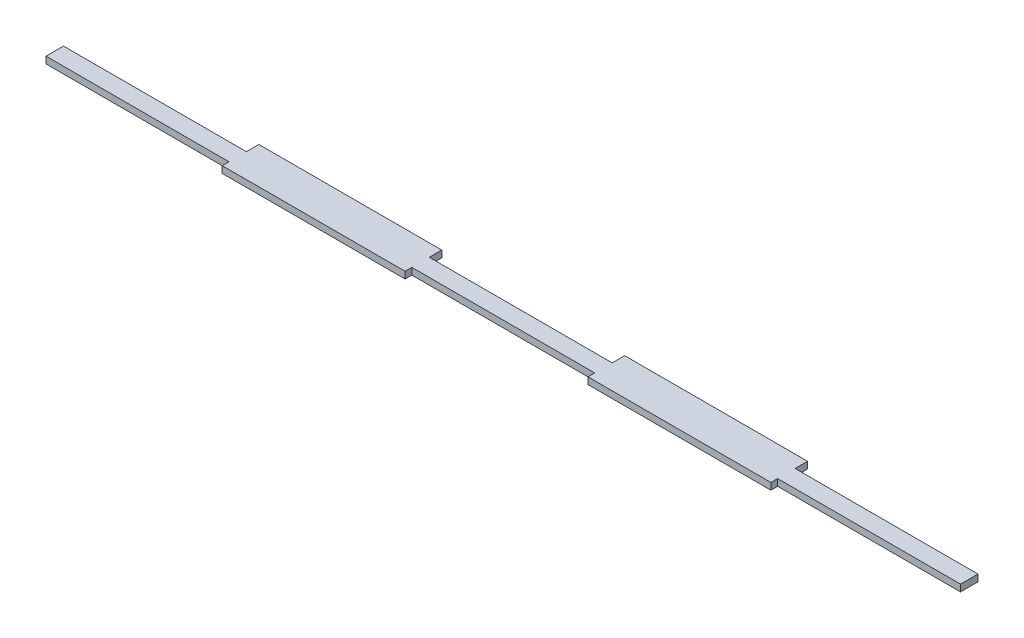
SolidWorks part; units mm, degrees
ref_plane "Front Plane" through (0, 0, 0) normal (0, 0, 1) x (1, 0, 0)
ref_plane "Top Plane" through (0, 0, 0) normal (0, 1, 0) x (1, 0, 0)
ref_plane "Right Plane" through (0, 0, 0) normal (1, 0, 0) x (0, 0, -1)
sketch "Sketch1" plane through (0, 0, 0) normal (0, 1, 0) x (1, 0, 0)
  line L0 (-183.2, 4.3294) -> (-109.92, 4.3294)
  line L2 (-183.2, 4.3294) -> (-183.2, -2.6706)
  line L3 (-109.92, -5.3706) -> (-36.64, -5.3706)
  line L4 (183.2, 4.3294) -> (183.2, -2.6706)
  line L5 (-183.2, -2.6706) -> (-109.92, -2.6706)
  line L6 (-109.92, 9.3294) -> (-36.64, 9.3294)
  line L8 (36.64, 9.3294) -> (109.92, 9.3294)
  line L10 (-109.92, 9.3294) -> (-109.92, 4.3294)
  line L11 (-36.64, 9.3294) -> (-36.64, 4.3294)
  line L12 (36.64, 9.3294) -> (36.64, 4.3294)
  line L13 (109.92, 9.3294) -> (109.92, 4.3294)
  line L14 (109.92, -5.3706) -> (109.92, -2.6706)
  line L15 (36.64, -5.3706) -> (36.64, -2.6706)
  line L16 (-36.64, -5.3706) -> (-36.64, -2.6706)
  line L17 (-109.92, -5.3706) -> (-109.92, -2.6706)
  line L18 (-36.64, 4.3294) -> (36.64, 4.3294)
  line L19 (-36.64, -2.6706) -> (36.64, -2.6706)
  line L20 (36.64, -5.3706) -> (109.92, -5.3706)
  line L21 (109.92, 4.3294) -> (183.2, 4.3294)
  line L22 (109.92, -2.6706) -> (183.2, -2.6706)
  point P0 (0, 0)
  dimension "D4" = 2.7
extrude "Boss-Extrude1" add sketch "Sketch1" along normal blind 2.7
